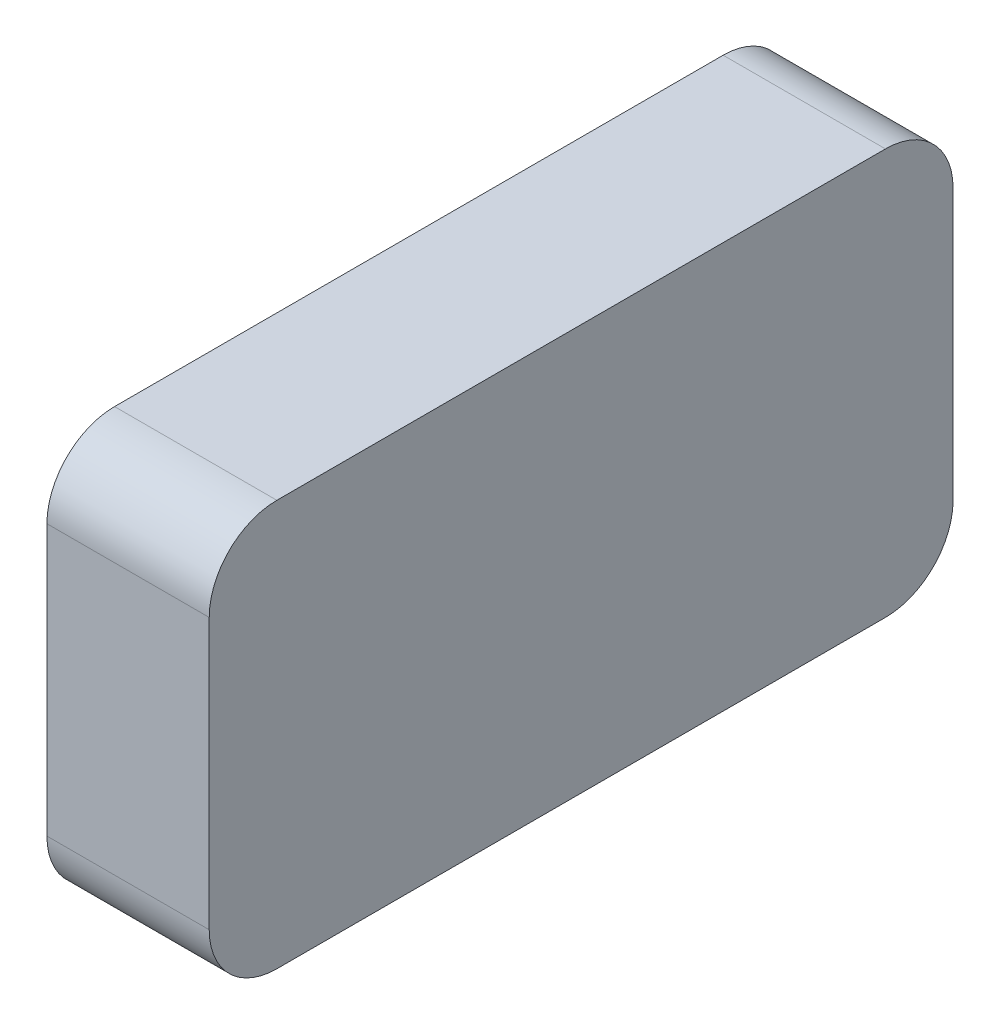
SolidWorks part; units mm, degrees
material "普通碳钢"
ref_plane "前视基准面" through (0, 0, 0) normal (0, 0, 1) x (1, 0, 0)
ref_plane "上视基准面" through (0, 0, 0) normal (0, 1, 0) x (1, 0, 0)
ref_plane "右视基准面" through (0, 0, 0) normal (1, 0, 0) x (0, 0, -1)
sketch "草图1" plane through (0, 0, 0) normal (1, 0, 0) x (0, 0, -1)
  line L1 (-22.5, 15) -> (22.5, 15)
  line L2 (-27.5, 10) -> (-27.5, -10)
  line L3 (-22.5, -15) -> (22.5, -15)
  line L4 (27.5, 10) -> (27.5, -10)
  line L5 (-27.5, 15) -> (27.5, -15) construction
  line L6 (-27.5, -15) -> (27.5, 15) construction
  arc A0 (22.5, 15) -> (27.5, 10) centre (22.5, 10) cw
  arc A1 (22.5, -15) -> (27.5, -10) centre (22.5, -10) ccw
  arc A2 (-22.5, -15) -> (-27.5, -10) centre (-22.5, -10) cw
  arc A3 (-27.5, 10) -> (-22.5, 15) centre (-22.5, 10) cw
  point P0 (0, 0)
  dimension "D3" = 5
  dimension "D1" = 55
  dimension "D2" = 30
extrude "凸台-拉伸1" add sketch "草图1" along normal blind 12
sketch "草图2" plane through (0, 0, 0) normal (-1, 0, 0) x (0, 0, 1)
  circle A1 centre (0, 0) radius 8
  dimension "D1" = 16
extrude "切除-拉伸1" cut sketch "草图2" against normal blind 8 contours A1
sketch "草图3" plane through (0, -15, 0) normal (0, -1, 0) x (1, 0, 0)
  line L0 (0, 0) -> (12, 0) construction
  line L1 (12, 22.5) -> (12, -22.5) construction
  circle A0 centre (3, 0) radius 2.5
  dimension "D1" = 5
  dimension "D2" = 3
extrude "切除-拉伸2" cut sketch "草图3" against normal blind 10
